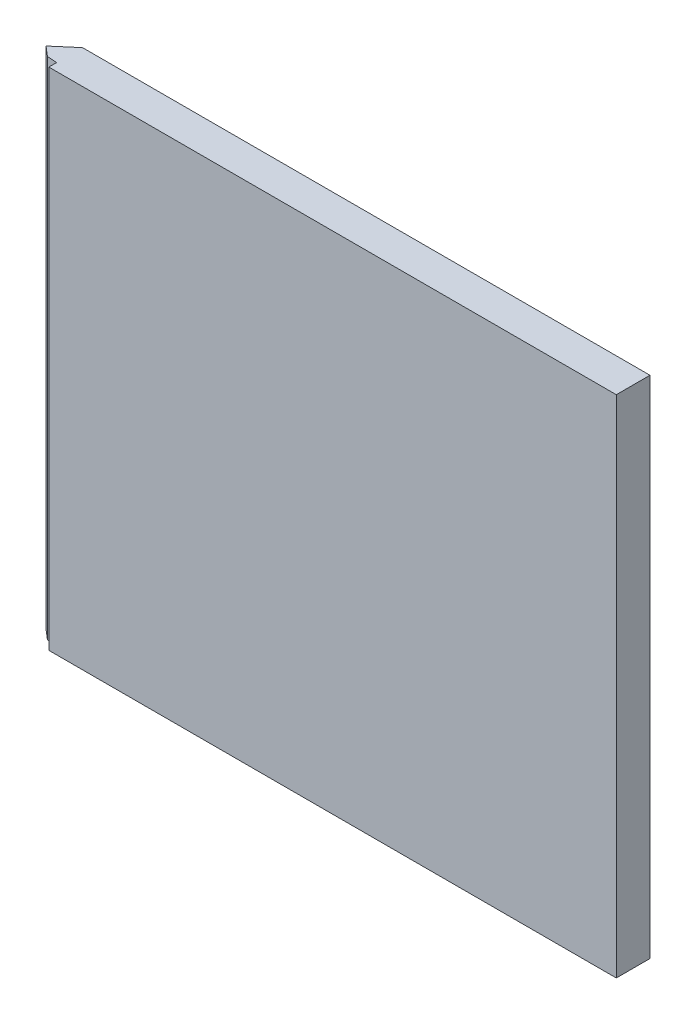
SolidWorks part; units mm, degrees
ref_plane "Plan de face" through (0, 0, 0) normal (0, 0, 1) x (1, 0, 0)
ref_plane "Plan de dessus" through (0, 0, 0) normal (0, 1, 0) x (1, 0, 0)
ref_plane "Plan de droite" through (0, 0, 0) normal (1, 0, 0) x (0, 0, -1)
sketch "Esquisse1" plane through (0, 0, 0) normal (0, 0, 1) x (1, 0, 0)
  line L1 (-52.6393, 28.8738) -> (51.9607, 28.8738)
  line L2 (-52.6393, 28.8738) -> (-52.6393, -61.1262)
  line L3 (-52.6393, -61.1262) -> (51.9607, -61.1262)
  line L4 (51.9607, 28.8738) -> (51.9607, -61.1262)
  dimension "D1" = 104.6
  dimension "D2" = 90
extrude "Boss.-Extru.3" add sketch "Esquisse1" along normal blind 6
sketch "Esquisse4" plane through (0, -61.1262, 0) normal (0, -1, 0) x (1, 0, 0)
  line L0 (-49.139, 6) -> (-52.6393, 6)
  line L1 (-52.6393, 6) -> (51.9607, 6) construction
  line L2 (-52.6393, 6) -> (-52.6393, 3)
  line L3 (-52.6393, 6) -> (-52.6393, 0) construction
  line L4 (-52.6393, 3) -> (-49.139, 6)
  dimension "D1" = 4.61
  dimension "D2" = 3
extrude "Enlèv. mat.-Extru.1" cut sketch "Esquisse4" against normal blind 91
sketch "Esquisse5" plane through (0, -61.1262, 0) normal (0, -1, 0) x (1, 0, 0)
  line L0 (-52.6393, 3) -> (-49.1393, 0)
  line L1 (-52.6393, 0) -> (51.9607, 0) construction
  line L2 (-49.1393, 0) -> (-52.6393, 0)
  line L3 (-52.6393, 0) -> (-52.6393, 3)
  dimension "D1" = 3.5
  dimension "D2" = 3
extrude "Enlèv. mat.-Extru.2" cut sketch "Esquisse5" against normal blind 91
sketch "Esquisse7" plane through (0, -61.1262, 0) normal (0, -1, 0) x (-1, 0, 0)
  line L0 (49.139, -6) -> (50.8891, -4.5)
  line L1 (52.6393, -3) -> (49.139, -6) construction
  line L2 (50.8891, -4.5) -> (49.139, -4.6198)
  line L3 (49.139, -4.6198) -> (49.139, -6)
extrude "Enlèv. mat.-Extru.4" cut sketch "Esquisse7" against normal blind 90
sketch "Esquisse8" plane through (0, 0, 6) normal (0, 0, 1) x (1, 0, 0)
  line L0 (-1.5736, -40.2282) -> (-3.2078, -40.5228)
  line L1 (18.3059, -50.2492) -> (-3.2078, -50.2492)
  line L2 (18.3059, -50.2492) -> (18.3059, -55.3885)
  line L3 (18.3059, -55.3885) -> (-3.2078, -55.3885)
  line L4 (-3.2078, -50.2492) -> (-3.2078, -55.3885)
  arc A0 (7.549, -50.2492) -> (-3.2078, -50.2492) centre (2.1706, -50.2492) ccw
  arc A1 (5.9149, -50.2492) -> (-1.5736, -50.2492) centre (2.1706, -50.2492) ccw
  arc A2 (-3.2078, -40.5228) -> (6.7627, -37.7228) centre (2.1706, -40.5228) cw
  arc A3 (-1.5736, -40.2282) -> (5.9149, -40.8173) centre (2.1706, -40.5228) cw
  dimension "D1" = 0
